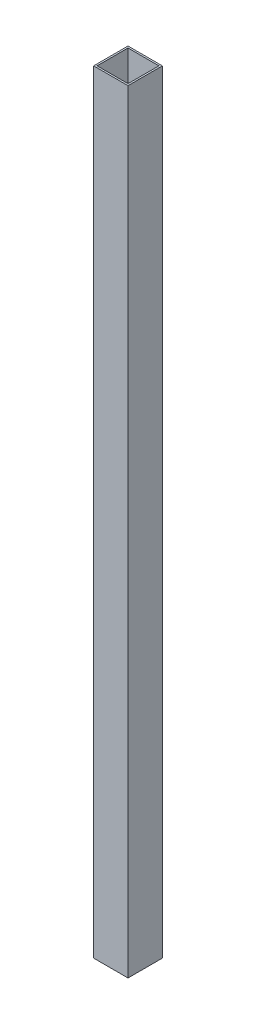
SolidWorks part; units mm, degrees
ref_plane "Alzado" through (0, 0, 0) normal (0, 0, 1) x (1, 0, 0)
ref_plane "Planta" through (0, 0, 0) normal (0, 1, 0) x (1, 0, 0)
ref_plane "Vista lateral" through (0, 0, 0) normal (1, 0, 0) x (0, 0, -1)
sketch "Croquis1" plane through (0, 0, 0) normal (0, 1, 0) x (1, 0, 0)
  line L1 (-20, -20) -> (20, -20)
  line L2 (-20, -20) -> (-20, 20)
  line L3 (-20, 20) -> (20, 20)
  line L4 (20, -20) -> (20, 20)
  line L5 (-20, -20) -> (20, 20) construction
  line L6 (-20, 20) -> (20, -20) construction
  point P0 (0, 0)
  dimension "D1" = 40
  dimension "D2" = 40
extrude "Saliente-Extruir1" add sketch "Croquis1" along normal blind 900
sketch "Croquis2" plane through (0, 900, 0) normal (0, 1, 0) x (1, 0, 0)
  line L0 (18, -18) -> (18, 18)
  line L1 (18, 18) -> (-18, 18)
  line L2 (-18, 18) -> (-18, -18)
  line L3 (-18, -18) -> (18, -18)
  line L4 (20, -20) -> (20, 20)
  line L5 (20, 20) -> (-20, 20)
  line L6 (-20, 20) -> (-20, -20)
  line L7 (-20, -20) -> (20, -20)
  line L8 (20, -20) -> (20, 20) construction
  line L9 (20, 20) -> (-20, 20) construction
  line L10 (-20, 20) -> (-20, -20) construction
  line L11 (-20, -20) -> (20, -20) construction
  dimension "D1" = 0
  dimension "D2" = 2
extrude "Cortar-Extruir1" cut sketch "Croquis2" against normal through all
